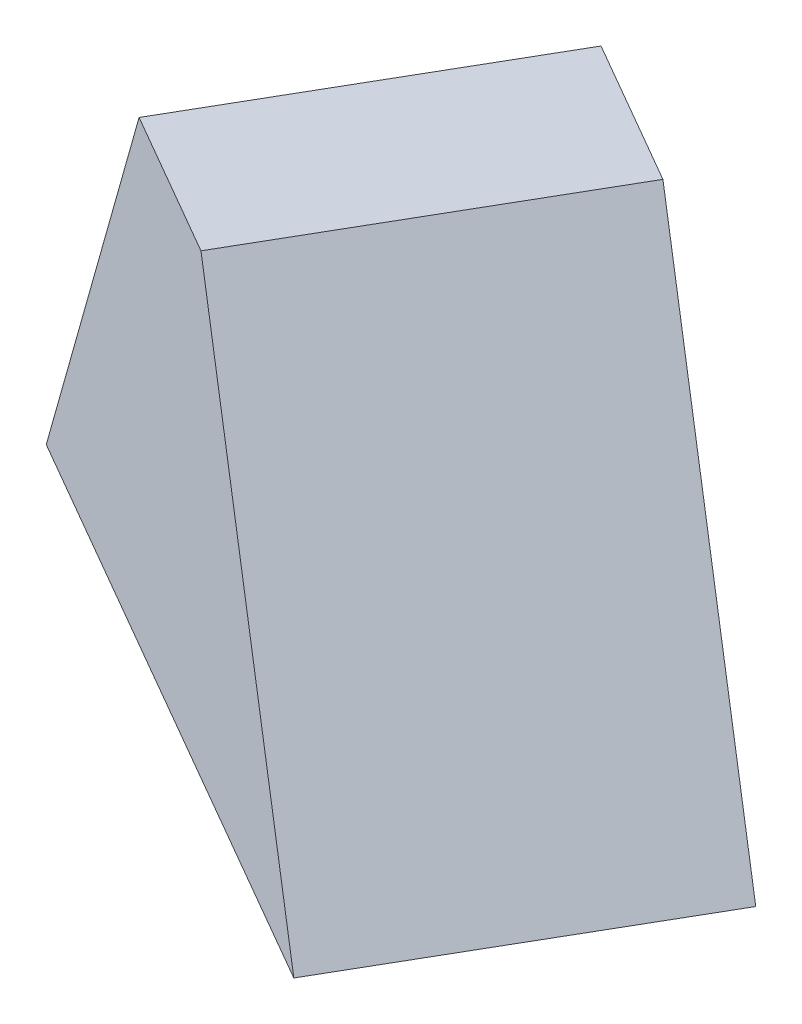
SolidWorks part; units mm, degrees
ref_plane "Front" through (0, 0, 0) normal (0, 0, 1) x (1, 0, 0)
ref_plane "Top" through (0, 0, 0) normal (0, 1, 0) x (1, 0, 0)
ref_plane "Right" through (0, 0, 0) normal (1, 0, 0) x (0, 0, -1)
sketch "Sketch1" plane through (0, 0, 0) normal (0, 1, 0) x (1, 0, 0)
  line L0 (-11.9047, -10) -> (-31.9047, -44.641)
  line L1 (-31.9047, -44.641) -> (37.3774, -84.641)
  line L2 (37.3774, -84.641) -> (57.3774, -50)
  line L3 (57.3774, -50) -> (-11.9047, -10)
  line L4 (-11.9047, -10) -> (75.6636, -10) construction
  dimension "D1" = 40
  dimension "D2" = 80
  dimension "D3" = 10
  dimension "D4" = 30
ref_plane "Plane1" through (0, 54, 0) normal (0, 1, 0) x (-1, 0, 0)
sketch "Sketch3" plane through (0, 54, 0) normal (0, 1, 0) x (-1, 0, 0)
  line L0 (-14.0761, 25) -> (5.9239, 59.641)
  line L1 (5.9239, 59.641) -> (-11.3966, 69.641)
  line L2 (-11.3966, 69.641) -> (-31.3966, 35)
  line L3 (-31.3966, 35) -> (-14.0761, 25)
  line L5 (11.9047, 10) -> (31.9047, 44.641) construction
  line L6 (-37.3774, 84.641) -> (-57.3774, 50) construction
  line L7 (-57.3774, 50) -> (11.9047, 10) construction
  dimension "D1" = 30
  dimension "D2" = 30
  dimension "D3" = 40
loft "Loft1" add profiles "Sketch3", "Sketch1"
sketch "Sketch4" plane through (0, 0, 0) normal (0, 0, 1) x (1, 0, 0)
  line L0 (-31.9047, 0) -> (-97.8383, 0) construction
  line L1 (11.3966, 54) -> (-67.9047, 0)
  dimension "D1" = 36
sketch "Sketch5" plane through (0, 0, 0) normal (0, 1, 0) x (1, 0, 0)
  line L0 (-67.9047, 0) -> (-22.5992, -78.4713)
  line L1 (-31.9047, 0) -> (-97.8383, 0) construction
  line L2 (11.3966, 0) -> (-67.9047, 0) construction
  dimension "D1" = 60
ref_plane "Cutting Plane" through (-19.4572, 28.5737, 11.2336) normal (-0.5353, 0.7861, 0.3091) x (-0.8447, -0.4982, -0.1959)
